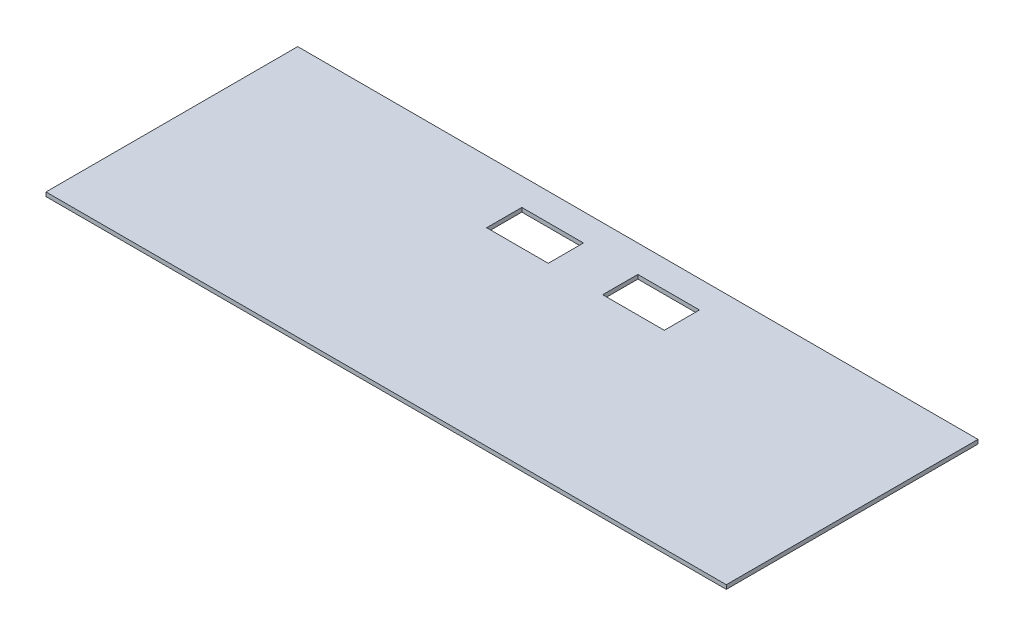
SolidWorks part; units mm, degrees
ref_plane "Front Plane" through (0, 0, 0) normal (0, 0, 1) x (1, 0, 0)
ref_plane "Top Plane" through (0, 0, 0) normal (0, 1, 0) x (1, 0, 0)
ref_plane "Right Plane" through (0, 0, 0) normal (1, 0, 0) x (0, 0, -1)
sketch "Sketch1" plane through (0, 0, 0) normal (0, 1, 0) x (1, 0, 0)
  line L2 (250, -95) -> (-250, -95)
  line L5 (-250, 90) -> (-250, -95)
  line L6 (250, 90) -> (-250, 90)
  line L7 (250, 90) -> (250, -95)
extrude "Boss-Extrude1" add sketch "Sketch1" along normal blind 3
sketch "Sketch2" plane through (0, 3, 0) normal (0, 1, 0) x (1, 0, 0)
  line L0 (0, 90) -> (0, 70)
  line L1 (250, 90) -> (-250, 90) construction
  line L2 (0, 70) -> (-20, 70)
  line L3 (0, 70) -> (20, 70)
  line L4 (-65.28, 70) -> (-65.28, 44.15)
  line L5 (-65.28, 44.15) -> (-20, 44.15)
  line L6 (-20, 44.15) -> (-20, 70)
  line L7 (-20, 70) -> (-65.28, 70)
  line L8 (20, 70) -> (20, 44.15)
  line L9 (20, 44.15) -> (65.28, 44.15)
  line L10 (65.28, 44.15) -> (65.28, 70)
  line L11 (65.28, 70) -> (20, 70)
extrude "Cut-Extrude1" cut sketch "Sketch2" against normal up to surface (3 mm away) contours L6 L7 L4 L5 | L10 L11 L8 L9 up to face at (0, 0, 2.5)
